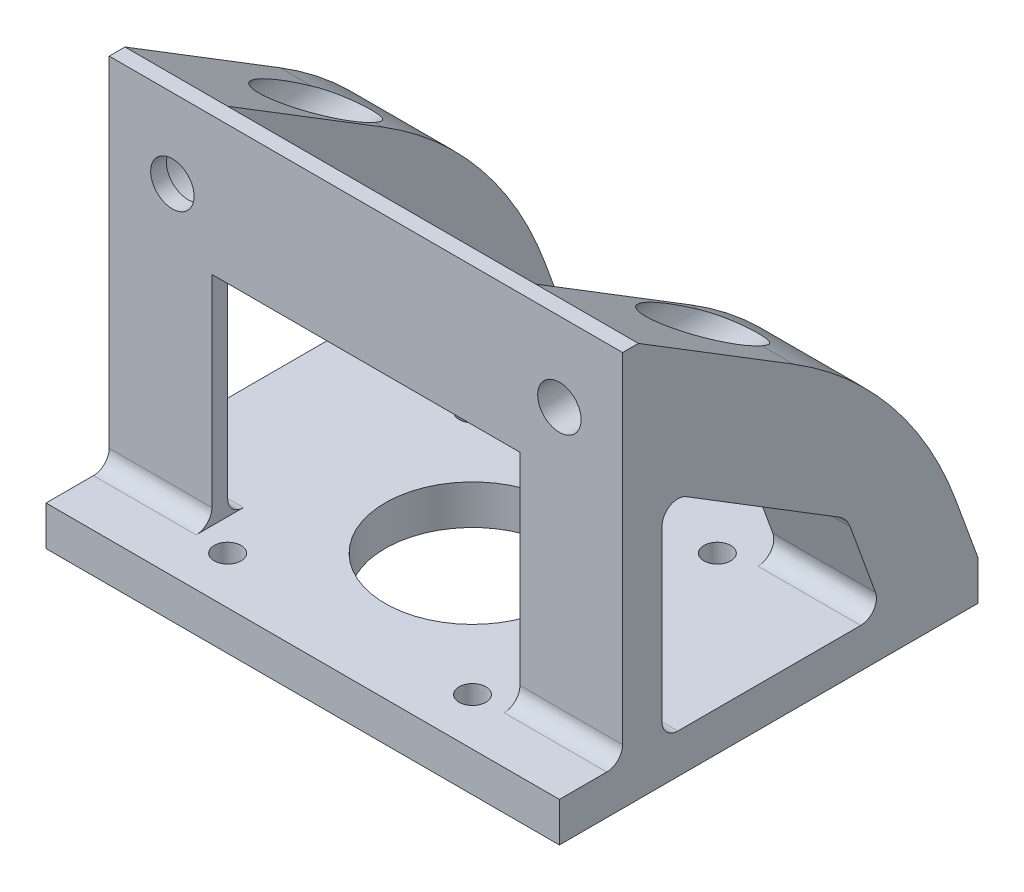
SolidWorks part; units mm, degrees
ref_plane "Front Plane" through (0, 0, 0) normal (0, 0, 1) x (1, 0, 0)
ref_plane "Top Plane" through (0, 0, 0) normal (0, 1, 0) x (1, 0, 0)
ref_plane "Right Plane" through (0, 0, 0) normal (1, 0, 0) x (0, 0, -1)
sketch "Sketch1" plane through (0, 0, 0) normal (1, 0, 0) x (0, 0, -1)
  line L0 (-11.5, 45) -> (-11.5, 0)
  line L1 (-11.5, 0) -> (21.5, 0)
  line L2 (21.5, 0) -> (21.5, -5)
  line L3 (21.5, -5) -> (-21.5, -5)
  line L4 (-13.5, 0) -> (-13.5, 45)
  line L5 (-13.5, 45) -> (-11.5, 45)
  line L6 (-13.5, 0) -> (-21.5, 0)
  line L7 (-21.5, 0) -> (-21.5, -5)
  line L9 (0, -5) -> (0, 0) construction
  dimension "D1" = 43
  dimension "D2" = 5
  dimension "D3" = 2
  dimension "D4" = 45
  dimension "D5" = 11.5
extrude "Boss-Extrude1" add sketch "Sketch1" along normal mid plane 65
sketch "Sketch2" plane through (0, -5, 0) normal (0, -1, 0) x (1, 0, 0)
  circle A0 centre (0, 0) radius 11.05
  dimension "D1" = 22.1
extrude "Cut-Extrude1" cut sketch "Sketch2" against normal blind 43
sketch "Sketch3" plane through (0, 0, 11.5) normal (0, 0, -1) x (-1, 0, 0)
  line L0 (-32.5, 45) -> (32.5, 45) construction
  line L1 (-11.5, 90) -> (11.5, 90)
  line L2 (-11.5, 90) -> (-11.5, 0)
  line L3 (-11.5, 0) -> (11.5, 0)
  line L4 (11.5, 90) -> (11.5, 0)
  line L5 (-11.5, 90) -> (11.5, 0) construction
  line L6 (-11.5, 0) -> (11.5, 90) construction
  line L7 (-32.5, 0) -> (32.5, 0) construction
  point P0 (0, 45)
  dimension "D1" = 23
extrude "Cut-Extrude2" cut sketch "Sketch3" against normal through all
hole_wizard "M5 Clearance Hole1" positions "Sketch4" profile "Sketch5" hole size "M5" standard "ISO" end condition through all
sketch "Sketch4" plane through (0, 0, 11.5) normal (0, 0, -1) x (-1, 0, 0)
  line L0 (-24.5, 45) -> (-24.5, 35) construction
  line L2 (-24.5, 35) -> (-11.5, 35) construction
  line L3 (-11.5, 0) -> (-11.5, 45) construction
  line L5 (0, 0) -> (0, 52.4528) construction
  line L7 (-32.5, 45) -> (-11.5, 45) construction
  point P0 (-24.5, 35)
  point P2 (24.5, 35)
  dimension "D1" = 10
  dimension "D2" = 13
sketch "Sketch5" plane through (24.5, 35, 11.5) normal (1, 0, 0) x (0, 1, 0)
  line L0 (0, 0) -> (0, 10)
  line L1 (0, 10) -> (2.75, 10)
  line L2 (2.75, 10) -> (2.75, 0)
  line L5 (2.75, 0) -> (0, 0)
  line L11 (0, -6.35) -> (0, 107.95) construction
  dimension "Thru Hole Dia." = 5.5
  dimension "Thru Hole Depth" = 10
hole_wizard "M3 Clearance Hole1" positions "Sketch7" profile "Sketch8" hole size "M3" standard "ISO" end condition through all
sketch "Sketch7" plane through (0, -5, 0) normal (0, -1, 0) x (-1, 0, 0)
  point P0 (-15.5, 15.5)
  point P3 (15.5, 15.5)
  point P6 (15.5, -15.5)
  point P9 (-15.5, -15.5)
sketch "Sketch8" plane through (15.5, -5, -15.5) normal (1, 0, 0) x (0, 0, -1)
  line L0 (0, 0) -> (0, 50)
  line L1 (0, 50) -> (1.7, 50)
  line L2 (1.7, 50) -> (1.7, 0)
  line L5 (1.7, 0) -> (0, 0)
  line L11 (0, -6.35) -> (0, 107.95) construction
  dimension "Thru Hole Dia." = 3.4
  dimension "Thru Hole Depth" = 50
sketch "Sketch9" plane through (0, 0, 11.5) normal (0, 0, -1) x (-1, 0, 0)
  line L0 (-32.5, 45) -> (-11.5, 45) construction
  line L1 (-11.5, 0) -> (-19.5, 0)
  line L2 (-11.5, 0) -> (-11.5, 45)
  line L3 (-11.5, 45) -> (-19.5, 45)
  line L4 (-19.5, 0) -> (-19.5, 45)
  dimension "D1" = 8
extrude "Cut-Extrude3" cut sketch "Sketch9" against normal blind 4
mirror "Mirror1" about plane through (0, 0, 0) normal (1, 0, 0) of "Cut-Extrude3"
sketch "Sketch6" plane through (32.5, 0, 0) normal (1, 0, 0) x (0, 0, -1)
  line L0 (-11.5, 45) -> (-11.5, 31.3636)
  line L1 (-11.5, 0) -> (-11.5, 45) construction
  line L2 (-11.5, 31.3636) -> (11.5, 0)
  line L3 (21.5, 0) -> (-11.5, 0) construction
  line L4 (11.5, 0) -> (21.5, 0)
  line L5 (21.5, 0) -> (-11.5, 45)
  dimension "D1" = 10
extrude "Boss-Extrude2" [suppressed] add sketch "Sketch6" against normal up to vertex
sketch "Sketch12" [suppressed] plane through (0, 0, 11.5) normal (0, 0, -1) x (-1, 0, 0)
  line L1 (-19.5, 31.3636) -> (19.5, 31.3636)
  line L2 (-19.5, 31.3636) -> (-19.5, 45)
  line L3 (-19.5, 45) -> (19.5, 45)
  line L4 (19.5, 31.3636) -> (19.5, 45)
extrude "Boss-Extrude3" [suppressed] add sketch "Sketch12" against normal blind 2
sketch "Sketch13" plane through (-32.5, 0, 0) normal (-1, 0, 0) x (0, 0, 1)
  line L0 (21.5, -5) -> (-21.5, -5) construction
  line L1 (-21.5, 0) -> (-31.5, 0)
  line L2 (-21.5, 0) -> (-21.5, -5)
  line L3 (-21.5, -5) -> (-31.5, -5)
  line L4 (-31.5, 0) -> (-31.5, -5)
  dimension "D1" = 10
extrude "Boss-Extrude4" add sketch "Sketch13" against normal up to vertex (65 mm away) up to point (32.5, -5, -21.5)
sketch "Sketch14" plane through (-32.5, 0, 0) normal (-1, 0, 0) x (0, 0, 1)
  line L0 (-19.5, 0) -> (-15.3185, 11.4887)
  line L1 (-31.5, 0) -> (11.5, 0) construction
  line L2 (-13.8647, 13.272) -> (11.5, 28.893)
  line L3 (11.5, 0) -> (11.5, 45) construction
  line L4 (11.5, 28.893) -> (11.5, 45)
  line L5 (11.5, 45) -> (-8.1321, 32.9094)
  line L6 (-28.7095, 7.6668) -> (-31.5, 0)
  line L7 (-31.5, 0) -> (-19.5, 0)
  arc A0 (-15.3185, 11.4887) -> (-13.8647, 13.272) centre (-12.0291, 10.2914) cw
  arc A1 (-8.1321, 32.9094) -> (-28.7095, 7.6668) centre (17.8503, -9.2796) ccw
  dimension "D1" = 12
  dimension "D2" = 70
extrude "Boss-Extrude5" add sketch "Sketch14" against normal up to vertex
mirror "Mirror4" about plane through (0, 0, 0) normal (1, 0, 0) of "Boss-Extrude5"
sketch "Sketch10" plane through (0, 0, 11.5) normal (0, 0, -1) x (-1, 0, 0)
  circle A0 centre (-24.5, 35) radius 4.5
  circle A1 centre (-24.5, 35) radius 2.75 construction
  dimension "D1" = 9
extrude "Cut-Extrude4" cut sketch "Sketch10" along normal through all
mirror "Mirror3" about plane through (0, 0, 0) normal (1, 0, 0) of "Cut-Extrude4"
sketch "Sketch15" plane through (32.5, 0, 0) normal (1, 0, 0) x (0, 0, -1)
  line L0 (-11.5, 0) -> (-8.5, 0)
  line L1 (19.5, 0) -> (-11.5, 0) construction
  line L2 (-8.5, 0) -> (-8.5, 27.0455)
  line L3 (13.8647, 13.272) -> (-11.5, 28.893) construction
  line L4 (-8.5, 27.0455) -> (-11.5, 28.893)
  line L5 (-11.5, 28.893) -> (-11.5, 0)
  dimension "D1" = 3
extrude "Boss-Extrude6" add sketch "Sketch15" against normal up to vertex
fillet "Fillet1" radius 2 8 edges at (-26, 0, 13.5) (26, 0, 13.5) (26, 27.0455, 8.5) (-26, 28.893, 11.5) (-26, 0, -19.5) (-26, 0, 11.5) (26, 0, -19.5) (26, 0, 8.5)
sketch "Sketch16" plane through (0, 0, 11.5) normal (0, 0, -1) x (-1, 0, 0)
  circle A0 centre (-24.5, 35) radius 2.75 construction
  circle A1 centre (-24.5, 35) radius 4.5
  circle A2 centre (-24.5, 35) radius 4.5
  circle A3 centre (-24.5, 35) radius 2.75
  dimension "D1" = 0
extrude "Boss-Extrude7" add sketch "Sketch16" along normal blind 5
mirror "Mirror5" about plane through (0, 0, 0) normal (1, 0, 0) of "Boss-Extrude7"
sketch "Sketch18" plane through (0, 0, 13.5) normal (0, 0, 1) x (1, 0, 0)
  line L0 (19.5, 45) -> (19.5, 2) construction
  line L1 (-19.5, 45) -> (19.5, 45)
  line L2 (-19.5, 45) -> (-19.5, 27.5682)
  line L3 (-19.5, 27.5682) -> (19.5, 27.5682)
  line L4 (19.5, 45) -> (19.5, 27.5682)
extrude "Boss-Extrude8" add sketch "Sketch18" against normal blind 2
mirror "Mirror2" about plane through (0, 0, 0) normal (1, 0, 0) of "Cut-Extrude4", "Boss-Extrude2"
sketch "Sketch11" plane through (-19.5, 0, 0) normal (1, 0, 0) x (0, 0, -1)
  line L0 (11.5, 0) -> (21.5, 0) construction
  line L1 (11.9007, 0) -> (7.9007, 0)
  line L2 (11.9007, 0) -> (11.9007, 14.4854)
  line L3 (11.9007, 14.4854) -> (7.9007, 14.4854)
  line L4 (7.9007, 0) -> (7.9007, 14.4854)
  line L5 (9.9007, 4.4) -> (9.9007, 14.4) construction
  dimension "D1" = 2
  dimension "D2" = 4
extrude "Cut-Extrude5" cut sketch "Sketch11" against normal through all
